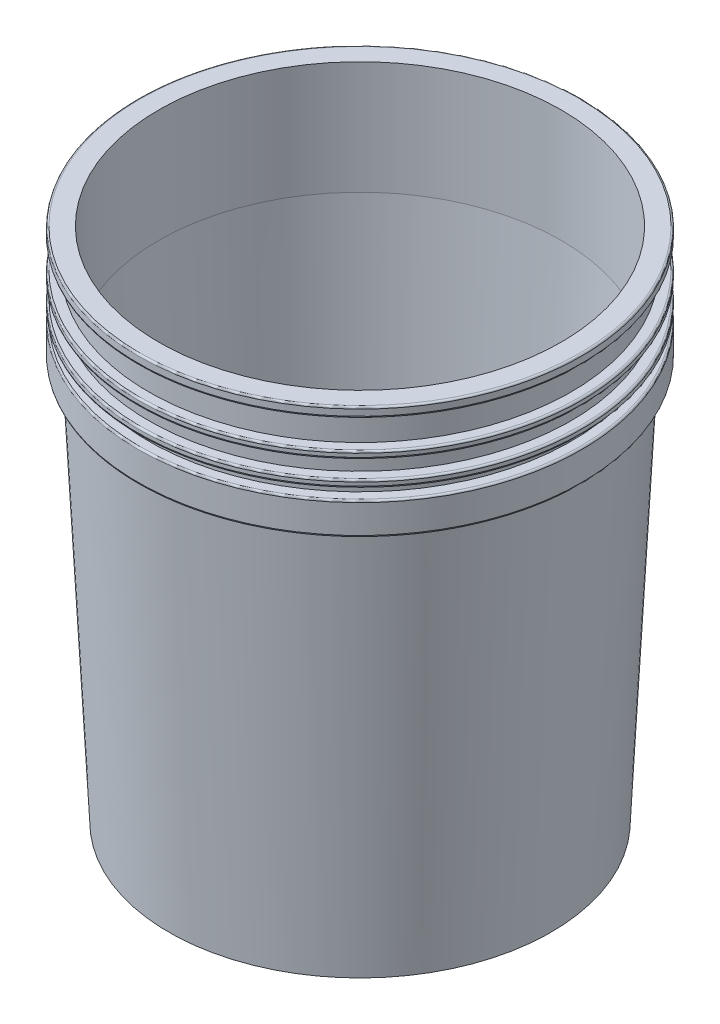
SolidWorks part; units mm, degrees
material "PE High Density"
ref_plane "Front Plane" through (0, 0, 0) normal (0, 0, 1) x (1, 0, 0)
ref_plane "Top Plane" through (0, 0, 0) normal (0, 1, 0) x (1, 0, 0)
ref_plane "Right Plane" through (0, 0, 0) normal (1, 0, 0) x (0, 0, -1)
sketch "Sketch1" plane through (0, 0, 0) normal (0, 0, 1) x (1, 0, 0)
  line L0 (0, 0) -> (0, 368.3) construction
  line L1 (0, 6.35) -> (25.4, 6.35)
  line L2 (25.4, 6.35) -> (25.4, 0)
  line L3 (25.4, 0) -> (32.4, 0)
  line L4 (32.4, 0) -> (32.4, 6.35)
  line L5 (32.4, 6.35) -> (129.6644, 6.35)
  line L6 (129.6644, 6.35) -> (129.3495, 0)
  line L7 (129.3495, 0) -> (136.3495, 0)
  line L11 (130.0114, 13.35) -> (0, 13.35)
  line L12 (0, 13.35) -> (0, 6.35)
  line L13 (143.6116, 368.3) -> (143.6116, 287.64)
  line L14 (143.6116, 287.64) -> (130.0114, 13.35)
  line L15 (143.6116, 368.3) -> (158.2316, 368.3)
  line L16 (158.2316, 368.3) -> (158.2316, 361.3)
  line L17 (158.2316, 361.3) -> (150.6116, 361.3)
  line L18 (150.6116, 361.3) -> (150.6116, 340.98)
  line L19 (150.6116, 340.98) -> (158.2316, 340.98)
  line L20 (158.2316, 340.98) -> (158.2316, 335.9)
  line L21 (158.2316, 335.9) -> (150.6116, 335.9)
  line L22 (150.6116, 335.9) -> (150.6116, 323.2)
  line L23 (150.6116, 323.2) -> (158.2316, 323.2)
  line L24 (158.2316, 323.2) -> (158.2316, 318.12)
  line L25 (158.2316, 318.12) -> (150.6116, 318.12)
  line L26 (150.6116, 318.12) -> (150.6116, 310.5)
  line L27 (150.6116, 310.5) -> (158.2316, 310.5)
  line L28 (158.2316, 310.5) -> (158.2316, 287.64)
  line L29 (158.2316, 287.64) -> (150.6116, 287.64)
  line L30 (150.6116, 287.64) -> (136.3495, 0)
  point P29 (155.9591, 309.2652)
  point P31 (156.3116, 320.4421)
  point P32 (154.9674, 320.1089)
  point P33 (149.9616, 319.6348)
  point P34 (149.9616, 319.7502)
  point P35 (0, 0)
  point P36 (143.6116, 319.1732)
  point P37 (0, 0)
  point P38 (143.6116, 285.75)
  point P39 (149.9616, 285.75)
  point P40 (151.5676, 0)
  point P41 (143.6116, 285.75)
  point P42 (156.3116, 363.22)
  point P43 (149.9616, 285.75)
  point P44 (143.6116, 285.75)
  point P45 (156.3116, 285.75)
  point P46 (149.9616, 311.15)
  point P47 (130.6937, 12.7)
  dimension "D1" = 368.3
  dimension "D3" = 287.2232
  dimension "D4" = 258.699
  dimension "D5" = 6.35
  dimension "D6" = 50.8
  dimension "D7" = 7
  dimension "D8" = 7.62
  dimension "D9" = 20.32
  dimension "D10" = 7
  dimension "D11" = 5.08
  dimension "D12" = 12.7
  dimension "D13" = 7.62
  dimension "D14" = 22.86
  dimension "D2" = 7
revolve "Revolve1" add sketch "Sketch1" angle 360 about L0
fillet "Fillet1" radius 1.27 8 edges at (0, 368.3, -158.2316) (0, 361.3, -158.2316) (0, 340.98, -158.2316) (0, 335.9, -158.2316) (0, 323.2, -158.2316) (0, 318.12, -158.2316) (0, 310.5, -158.2316) (0, 287.64, -158.2316)
equation "\"D2@Sketch1\"=\"D7@Sketch1\""
